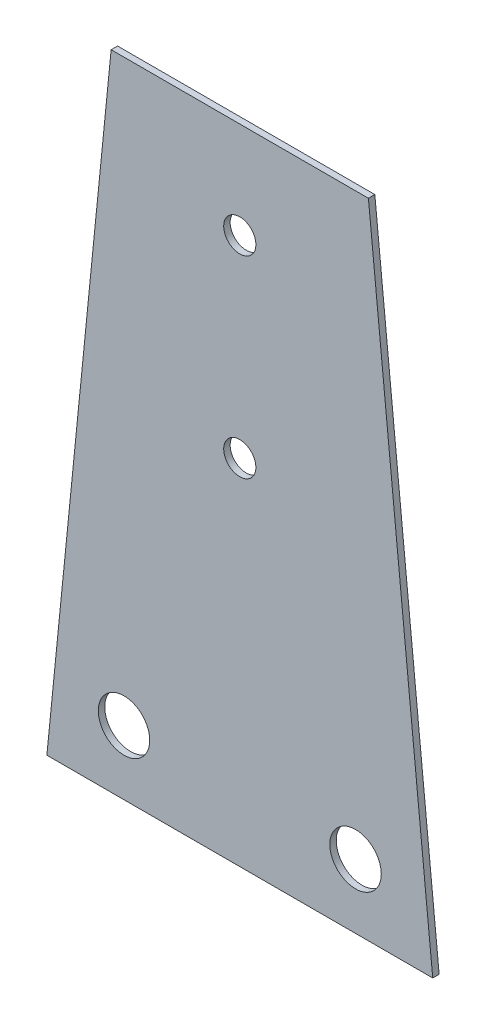
SolidWorks part; units mm, degrees
ref_plane "Front Plane" through (0, 0, 0) normal (0, 0, 1) x (1, 0, 0)
ref_plane "Top Plane" through (0, 0, 0) normal (0, 1, 0) x (1, 0, 0)
ref_plane "Right Plane" through (0, 0, 0) normal (1, 0, 0) x (0, 0, -1)
sketch "Sketch2" plane through (0, 0, 0) normal (0, 0, 1) x (1, 0, 0)
  line L0 (-20, 75.1803) -> (20, 75.1803)
  line L1 (20, 75.1803) -> (30, -24.8197)
  line L2 (30, -24.8197) -> (-30, -24.8197)
  line L3 (-30, -24.8197) -> (-20, 75.1803)
  point P2 (0, -24.8197)
  point P5 (0, 75.1803)
  dimension "D1" = 40
  dimension "D2" = 60
  dimension "D3" = 100
extrude "Boss-Extrude1" add sketch "Sketch2" along normal blind 1
sketch "Sketch3" plane through (0, 0, 1) normal (0, 0, 1) x (1, 0, 0)
  line L0 (34.2715, -4.8197) -> (-43.7701, -4.8197) construction
  line L1 (-30, -24.8197) -> (30, -24.8197) construction
  line L2 (34.2715, -14.8197) -> (-43.7701, -14.8197) construction
  line L4 (20, 75.1803) -> (-20, 75.1803) construction
  circle A0 centre (18, -14.8197) radius 4
  circle A1 centre (-18, -14.8197) radius 4
  circle A2 centre (0, 60.1803) radius 2.5
  circle A3 centre (0, 30.1803) radius 2.5
  point P15 (0, 0)
  dimension "D3" = 8
  dimension "D4" = 8
  dimension "D5" = 10
  dimension "D6" = 10
  dimension "D7" = 18
  dimension "D9" = 5
  dimension "D10" = 5
  dimension "D11" = 15
  dimension "D12" = 30
  dimension "D1" = 20
  dimension "D2" = 10
  dimension "D8" = 18
extrude "Cut-Extrude1" cut sketch "Sketch3" against normal through all
